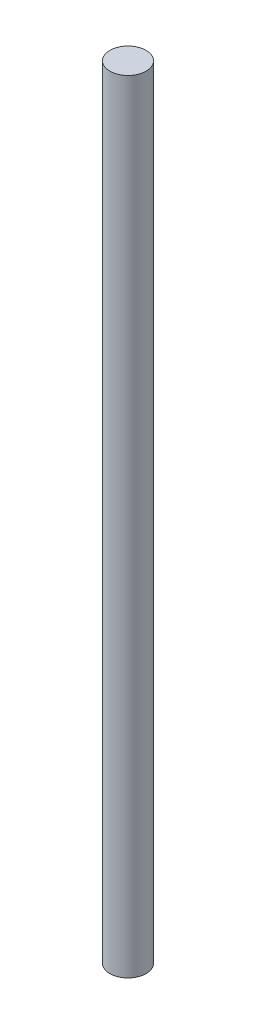
SolidWorks part; units mm, degrees
ref_plane "Front Plane" through (0, 0, 0) normal (0, 0, 1) x (1, 0, 0)
ref_plane "Top Plane" through (0, 0, 0) normal (0, 1, 0) x (1, 0, 0)
ref_plane "Right Plane" through (0, 0, 0) normal (1, 0, 0) x (0, 0, -1)
sketch "Sketch2" plane through (0, 0, 0) normal (0, 1, 0) x (1, 0, 0)
  circle A0 centre (0, 0) radius 1.825
  dimension "D1" = 3.65
extrude "Boss-Extrude1" add sketch "Sketch2" along normal blind 79
